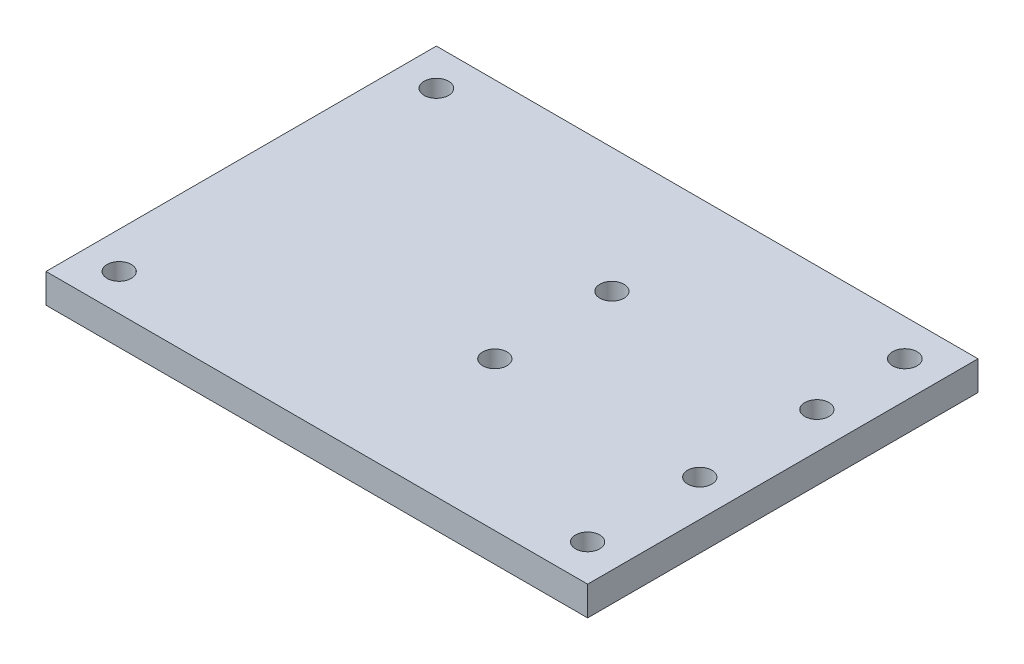
SolidWorks part; units mm, degrees
material "PC High Viscosity"
ref_plane "Front Plane" through (0, 0, 0) normal (0, 0, 1) x (1, 0, 0)
ref_plane "Top Plane" through (0, 0, 0) normal (0, 1, 0) x (1, 0, 0)
ref_plane "Right Plane" through (0, 0, 0) normal (1, 0, 0) x (0, 0, -1)
sketch "Sketch1" plane through (0, 0, 0) normal (0, 1, 0) x (1, 0, 0)
  line L0 (7.9375, 7.9375) -> (109.5375, 7.9375) construction
  line L1 (0, 0) -> (117.475, 0)
  line L2 (0, 0) -> (0, 84.6689)
  line L3 (0, 84.6689) -> (117.475, 84.6689)
  line L4 (117.475, 0) -> (117.475, 84.6689)
  line L5 (7.9375, 7.9375) -> (7.9375, 76.7314) construction
  line L6 (58.7375, 7.9375) -> (58.7375, 79.2321) construction
  circle A0 centre (7.9375, 7.9375) radius 2.6289
  circle A1 centre (109.5375, 7.9375) radius 2.6289
  circle A2 centre (7.9375, 76.7314) radius 2.667
  circle A3 centre (109.5375, 76.7314) radius 2.667
  point P13 (68.3946, 78.575)
  dimension "D1" = 7.9375
  dimension "D2" = 7.9375
  dimension "D3" = 5.2578
  dimension "D5" = 5.2578
  dimension "D8" = 5.334
  dimension "D4" = 101.6
  dimension "D6" = 7.9375
  dimension "D7" = 68.7939
  dimension "D9" = 7.9375
extrude "Boss-Extrude1" add sketch "Sketch1" along normal blind 6.35
sketch "Sketch2" plane through (0, 6.35, 0) normal (0, 1, 0) x (1, 0, 0)
  line L0 (117.475, 0) -> (117.475, 84.6689) construction
  line L1 (65.0875, 32.2568) -> (109.5375, 32.2568) construction
  line L2 (65.0875, 32.2568) -> (65.0875, 57.6568) construction
  line L3 (65.0875, 57.6568) -> (109.5375, 57.6568) construction
  line L4 (109.5375, 32.2568) -> (109.5375, 57.6568) construction
  line L5 (117.475, 84.6689) -> (0, 84.6689) construction
  circle A0 centre (109.5375, 32.2568) radius 2.6289
  circle A1 centre (109.5375, 57.6568) radius 2.6289
  circle A2 centre (65.0875, 57.6568) radius 2.6289
  circle A3 centre (65.0875, 32.2568) radius 2.6289
  dimension "D3" = 5.2578
  dimension "D4" = 5.2578
  dimension "D5" = 5.2578
  dimension "D6" = 5.2578
  dimension "D1" = 25.4
  dimension "D2" = 44.45
  dimension "D7" = 7.9375
  dimension "D8" = 27.0121
extrude "Cut-Extrude1" cut sketch "Sketch2" against normal through all
